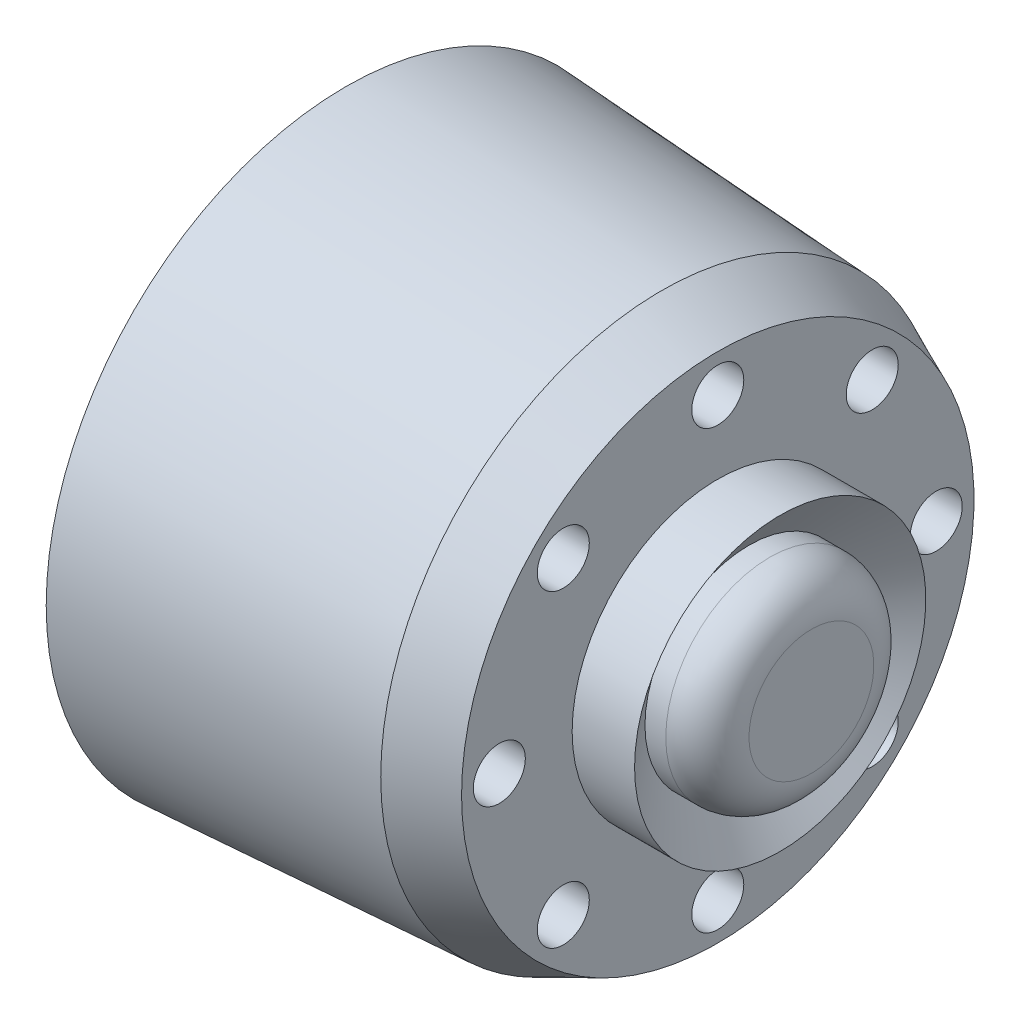
SolidWorks part; units mm, degrees
ref_plane "Front Plane" through (0, 0, 0) normal (0, 0, 1) x (1, 0, 0)
ref_plane "Top Plane" through (0, 0, 0) normal (0, 1, 0) x (1, 0, 0)
ref_plane "Right Plane" through (0, 0, 0) normal (1, 0, 0) x (0, 0, -1)
sketch "Sketch1" plane through (0, 0, 0) normal (0, 1, 0) x (1, 0, 0)
  line L0 (-18.2338, 0) -> (23.1429, 0) construction
  line L2 (11.6939, 12.315) -> (11.6939, 7)
  line L5 (-6.185, 0) -> (-6.185, 14.4)
  line L7 (11.6939, 7) -> (14.6939, 7)
  line L10 (14.6939, 5) -> (16.1939, 5)
  line L11 (16.1939, 5) -> (16.1939, 0)
  line L12 (-6.185, 0) -> (16.1939, 0)
  line L13 (-6.185, 14.4) -> (8.9939, 13.5)
  line L14 (8.9939, 13.5) -> (11.6939, 12.315)
  line L15 (14.6939, 7) -> (13.1939, 5)
  line L16 (13.1939, 5) -> (14.6939, 5)
  dimension "D1" = 24.63
  dimension "D2" = 28.8
  dimension "D3" = 2.7
  dimension "D4" = 14
  dimension "D5" = 3
  dimension "D6" = 1.5
  dimension "D7" = 10
  dimension "D8" = 27
  dimension "D11" = 1.5
revolve "Revolve1" add sketch "Sketch1" angle 360 about L0
sketch "Sketch2" plane through (-6.185, 0, 0) normal (-1, 0, 0) x (0, 0, 1)
  circle A0 centre (0, 0) radius 4.725
  dimension "D1" = 9.45
extrude "Cut-Extrude1" cut sketch "Sketch2" against normal offset from surface (7 mm away) 7 up to face at (-6.185, 0, 14.4)
sketch "Sketch3" plane through (11.6939, 0, 0) normal (1, 0, 0) x (0, 0, -1)
  circle A0 centre (0, 0) radius 10.5 construction
  circle A1 centre (0, 10.5) radius 1.25
  circle A2 centre (7.4246, 7.4246) radius 1.25
  circle A3 centre (10.5, 0) radius 1.25
  circle A4 centre (7.4246, -7.4246) radius 1.25
  circle A5 centre (0, -10.5) radius 1.25
  circle A6 centre (-7.4246, -7.4246) radius 1.25
  circle A7 centre (-10.5, 0) radius 1.25
  circle A8 centre (-7.4246, 7.4246) radius 1.25
  point P22 (0, 0)
  dimension "D1" = 21
  dimension "D2" = 2.5
  dimension "D3" = 8
extrude "Cut-Extrude2" cut sketch "Sketch3" against normal through all
sketch "Sketch4" plane through (-6.185, 0, 0) normal (-1, 0, 0) x (0, 0, 1)
  circle A0 centre (0, 0) radius 10.5 construction
  circle A1 centre (0, 10.5) radius 2.5
  circle A2 centre (7.4246, 7.4246) radius 2.5
  circle A3 centre (10.5, 0) radius 2.5
  circle A4 centre (7.4246, -7.4246) radius 2.5
  circle A5 centre (0, -10.5) radius 2.5
  circle A6 centre (-7.4246, -7.4246) radius 2.5
  circle A7 centre (-10.5, 0) radius 2.5
  circle A8 centre (-7.4246, 7.4246) radius 2.5
  point P22 (0, 0)
  dimension "D1" = 21
  dimension "D2" = 5
  dimension "D3" = 8
extrude "Cut-Extrude3" cut sketch "Sketch4" against normal offset from surface (14.8788 mm away) 3 up to face at (11.6939, 10.5, -1.25)
fillet "Fillet1" radius 2 1 edges at (16.1939, 0, 5)
